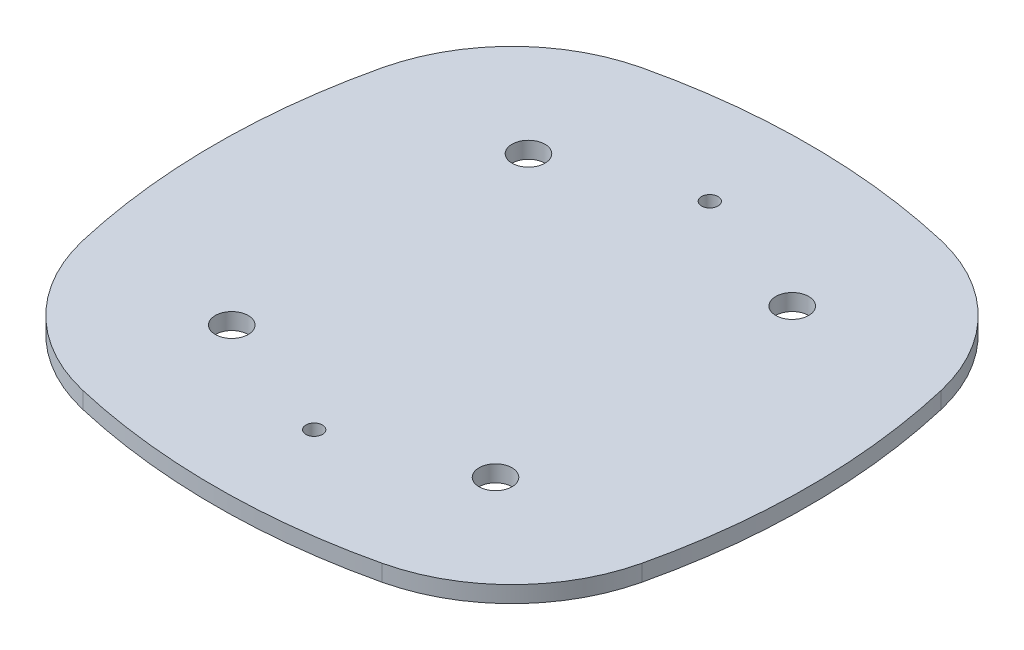
SolidWorks part; units mm, degrees
material "Ceramic Porcelain"
ref_plane "Front Plane" through (0, 0, 0) normal (0, 0, 1) x (1, 0, 0)
ref_plane "Top Plane" through (0, 0, 0) normal (0, 1, 0) x (1, 0, 0)
ref_plane "Right Plane" through (0, 0, 0) normal (1, 0, 0) x (0, 0, -1)
ref_plane "Plane1" through (0, 0, 0) normal (0, 1, 0) x (1, 0, 0)
sketch "Sketch1" plane through (0, 0, 0) normal (0, 1, 0) x (1, 0, 0)
  arc A0 (8.4782, -4.5385) -> (8.4782, 4.5385) centre (-11, 0) ccw
  arc A1 (-4.5385, -8.4782) -> (4.5385, -8.4782) centre (0, 11) ccw
  arc A2 (-8.4782, 4.5385) -> (-8.4782, -4.5385) centre (11, 0) ccw
  arc A3 (4.5385, 8.4782) -> (-4.5385, 8.4782) centre (0, -11) ccw
  arc A4 (8.4782, 4.5385) -> (4.5385, 8.4782) centre (3.3417, 3.3417) ccw
  arc A5 (-4.5385, 8.4782) -> (-8.4782, 4.5385) centre (-3.3417, 3.3417) ccw
  arc A6 (-8.4782, -4.5385) -> (-4.5385, -8.4782) centre (-3.3417, -3.3417) ccw
  arc A7 (4.5385, -8.4782) -> (8.4782, -4.5385) centre (3.3417, -3.3417) ccw
  circle A8 centre (4, 4.5) radius 0.5
  circle A9 centre (-4, 4.5) radius 0.5
  circle A10 centre (4, -4.5) radius 0.5
  circle A11 centre (-4, -4.5) radius 0.5
  circle A12 centre (0, 6) radius 0.25
  circle A13 centre (0, -6) radius 0.25
extrude "Extrude1" add sketch "Sketch1" along normal blind 0.5
